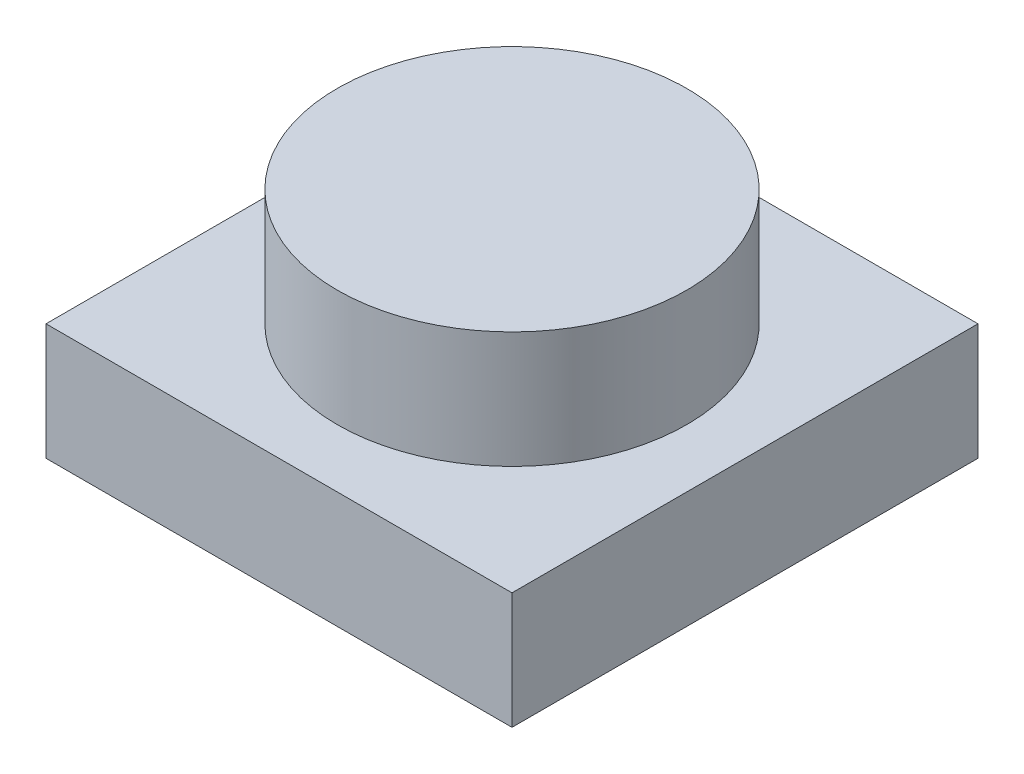
SolidWorks part; units mm, degrees
ref_plane "前视基准面" through (0, 0, 0) normal (0, 0, 1) x (1, 0, 0)
ref_plane "上视基准面" through (0, 0, 0) normal (0, 1, 0) x (1, 0, 0)
ref_plane "右视基准面" through (0, 0, 0) normal (1, 0, 0) x (0, 0, -1)
sketch "草图1" plane through (0, 0, 0) normal (0, 1, 0) x (1, 0, 0)
  line L1 (4, -4) -> (-4, -4)
  line L2 (4, -4) -> (4, 4)
  line L3 (4, 4) -> (-4, 4)
  line L4 (-4, -4) -> (-4, 4)
  line L5 (4, -4) -> (-4, 4) construction
  line L6 (4, 4) -> (-4, -4) construction
  point P0 (0, 0)
  dimension "D1" = 8
  dimension "D2" = 8
extrude "凸台-拉伸1" add sketch "草图1" along normal blind 2
sketch "草图2" plane through (0, 2, 0) normal (0, 1, 0) x (1, 0, 0)
  circle A0 centre (0, 0) radius 3
  dimension "D1" = 6
extrude "凸台-拉伸2" add sketch "草图2" along normal blind 2
